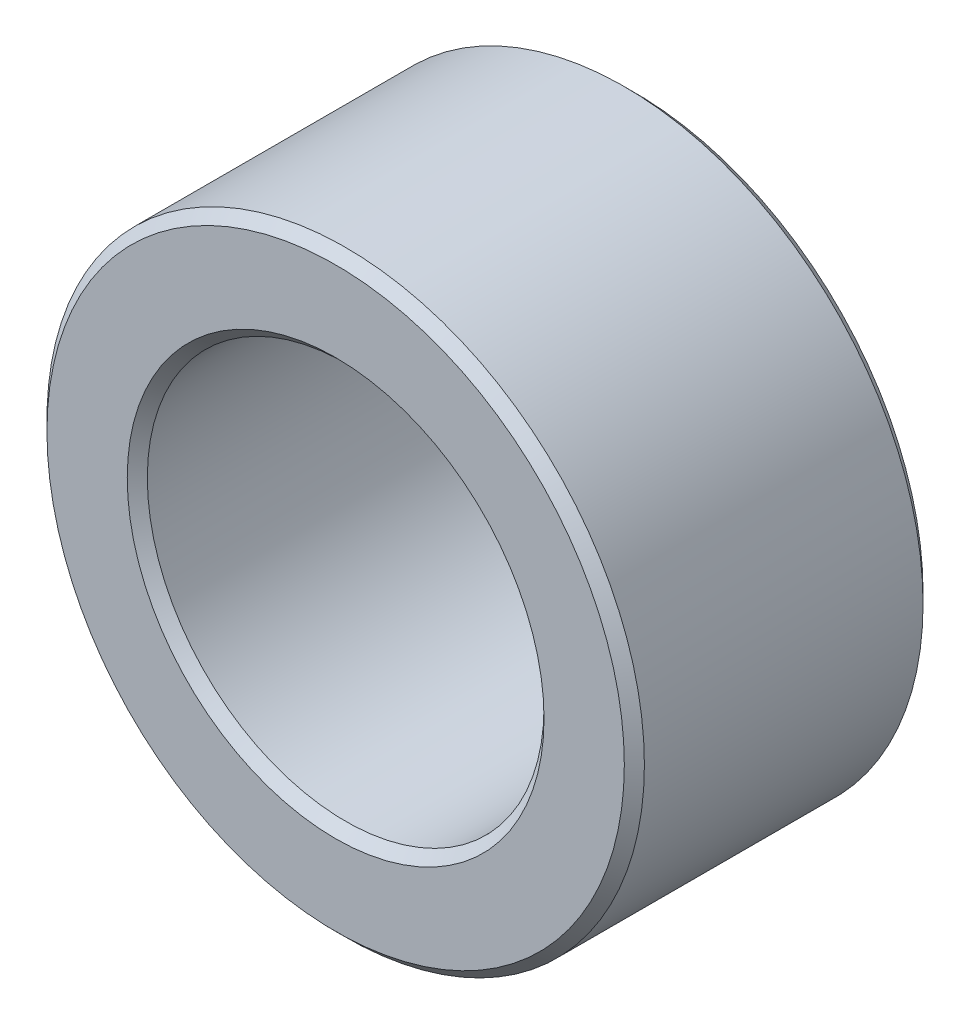
SolidWorks part; units mm, degrees
material "6061 Alloy"
ref_plane "Front Plane" through (0, 0, 0) normal (0, 0, 1) x (1, 0, 0)
ref_plane "Top Plane" through (0, 0, 0) normal (0, 1, 0) x (1, 0, 0)
ref_plane "Right Plane" through (0, 0, 0) normal (1, 0, 0) x (0, 0, -1)
sketch "Sketch1" plane through (0, 0, 0) normal (0, 0, 1) x (1, 0, 0)
  circle A0 centre (0, 0) radius 3.175 construction
  circle A1 centre (0, 0) radius 2.1082 construction
  point P4 (0, 3.175)
  dimension "ID" = 4.2164
  dimension "OD" = 6.35
sketch "Sketch2" plane through (0, 0, 0) normal (1, 0, 0) x (0, 0, -1)
  line L0 (-1.5875, 3.175) -> (1.5875, 3.175) construction
  dimension "Length" = 3.175
sketch "Sketch3" plane through (0, 0, 0) normal (0, 0, 1) x (1, 0, 0)
  circle A0 centre (0, 0) radius 2.1082 construction
  circle A1 centre (0, 0) radius 3.175 construction
  circle A2 centre (0, 0) radius 2.1082
  circle A3 centre (0, 0) radius 3.175
extrude "Boss-Extrude1" add sketch "Sketch3" against normal up to vertex (1.5875 mm away) and the other way up to vertex (1.5875 mm away) up to point (0, 3.175, -1.5875) other way up to point (0, 3.175, 1.5875)
chamfer "Chamfer1" distance 0.1067 angle 45 1 edges at (3.175, 0, 1.5875)
equation "\"D1@Chamfer1\"=(\"OD@Sketch1\"-\"ID@Sketch1\")*0.05"
